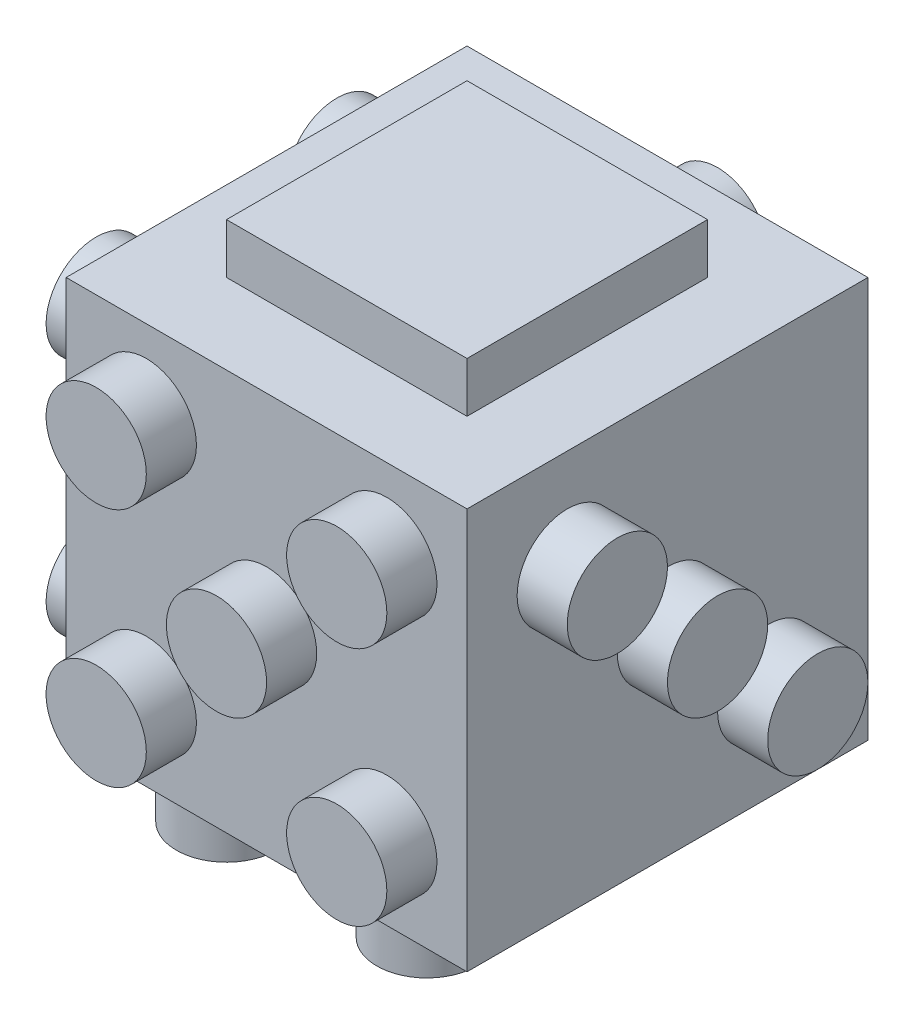
SolidWorks part; units mm, degrees
ref_plane "Front Plane" through (0, 0, 0) normal (0, 0, 1) x (1, 0, 0)
ref_plane "Top Plane" through (0, 0, 0) normal (0, 1, 0) x (1, 0, 0)
ref_plane "Right Plane" through (0, 0, 0) normal (1, 0, 0) x (0, 0, -1)
sketch "Sketch1" plane through (0, 0, 0) normal (0, 1, 0) x (1, 0, 0)
  line L1 (-12.5, 12.5) -> (12.5, 12.5)
  line L2 (-12.5, 12.5) -> (-12.5, -12.5)
  line L3 (-12.5, -12.5) -> (12.5, -12.5)
  line L4 (12.5, 12.5) -> (12.5, -12.5)
  line L5 (0, -12.5) -> (0, 12.5) construction
  line L6 (-12.5, 0) -> (12.5, 0) construction
  point P0 (0, 0)
  dimension "D1" = 25
  dimension "D2" = 25
extrude "Boss-Extrude1" add sketch "Sketch1" along normal blind 25
sketch "Sketch2" plane through (0, 25, 0) normal (0, 1, 0) x (1, 0, 0)
  line L1 (-6, 6) -> (6, 6)
  line L2 (-6, 6) -> (-6, -6)
  line L3 (-6, -6) -> (6, -6)
  line L4 (6, 6) -> (6, -6)
  line L5 (0, -6) -> (0, 6) construction
  line L6 (-6, 0) -> (6, 0) construction
  point P0 (0, 0)
  dimension "D1" = 12
  dimension "D2" = 12
sketch "Sketch3" plane through (0, 0, 0) normal (0, -1, 0) x (1, 0, 0)
  line L1 (10, 10) -> (-10, 10) construction
  line L2 (10, 10) -> (10, -10) construction
  line L3 (10, -10) -> (-10, -10) construction
  line L4 (-10, 10) -> (-10, -10) construction
  line L5 (0, -10) -> (0, 10) construction
  line L6 (10, 0) -> (-10, 0) construction
  line L7 (5, -7) -> (-5, -7) construction
  line L8 (5, -7) -> (5, 7) construction
  line L9 (5, 7) -> (-5, 7) construction
  line L10 (-5, -7) -> (-5, 7) construction
  line L11 (0, 7) -> (0, -7) construction
  line L12 (5, 0) -> (-5, 0) construction
  circle A0 centre (-5, 7) radius 2.5
  circle A1 centre (-5, 0) radius 2.5
  circle A2 centre (-5, -7) radius 2.5
  circle A3 centre (5, 7) radius 2.5
  circle A4 centre (5, 0) radius 2.5
  circle A5 centre (5, -7) radius 2.5
  point P0 (0, 0)
  point P4 (0, 0)
  dimension "D5" = 5
  dimension "D6" = 5
  dimension "D7" = 5
  dimension "D8" = 5
  dimension "D1" = 20
  dimension "D2" = 20
  dimension "D3" = 10
  dimension "D4" = 14
sketch "Sketch4" plane through (12.5, 0, 0) normal (1, 0, 0) x (0, 0, -1)
  line L4 (-12.5, 0) -> (12.5, 0)
  line L5 (12.5, 0) -> (12.5, 25)
  line L6 (12.5, 25) -> (-12.5, 25)
  line L7 (-12.5, 25) -> (-12.5, 0)
  line L8 (-12.5, 0) -> (12.5, 0)
  line L10 (12.5, 25) -> (-12.5, 25)
  line L11 (-12.5, 25) -> (-12.5, 0)
  circle A0 centre (-5, 17.5) radius 2.5
  circle A1 centre (0, 12.5) radius 2.5
  circle A2 centre (5, 7.5) radius 2.5
  dimension "D5" = 5
  dimension "D6" = 5
  dimension "D7" = 5
  dimension "D1" = 0
sketch "Sketch5" plane through (-12.5, 0, 0) normal (-1, 0, 0) x (0, 0, 1)
  line L0 (-12.5, 12.5) -> (0, 12.5) construction
  line L2 (-10, 22.5) -> (10, 22.5) construction
  line L3 (-10, 22.5) -> (-10, 2.5) construction
  line L4 (-12.5, 0) -> (12.5, 0)
  line L5 (12.5, 0) -> (12.5, 25)
  line L6 (12.5, 25) -> (-12.5, 25)
  line L7 (-12.5, 25) -> (-12.5, 0)
  line L8 (-12.5, 0) -> (12.5, 0)
  line L9 (12.5, 0) -> (12.5, 25)
  line L10 (12.5, 25) -> (-12.5, 25)
  line L11 (-12.5, 25) -> (-12.5, 0)
  line L12 (-10, 2.5) -> (10, 2.5) construction
  line L13 (10, 22.5) -> (10, 2.5) construction
  line L14 (0, 2.5) -> (0, 22.5) construction
  line L15 (-10, 12.5) -> (10, 12.5) construction
  line L16 (-6, 18.5) -> (6, 18.5) construction
  line L17 (-6, 18.5) -> (-6, 6.5) construction
  line L18 (-6, 6.5) -> (6, 6.5) construction
  line L19 (6, 18.5) -> (6, 6.5) construction
  line L20 (0, 6.5) -> (0, 18.5) construction
  line L21 (-6, 12.5) -> (6, 12.5) construction
  circle A0 centre (-6, 18.5) radius 2.5
  circle A1 centre (6, 18.5) radius 2.5
  circle A2 centre (6, 6.5) radius 2.5
  circle A3 centre (-6, 6.5) radius 2.5
  dimension "D6" = 5
  dimension "D7" = 5
  dimension "D8" = 5
  dimension "D9" = 5
  dimension "D2" = 20
  dimension "D3" = 20
  dimension "D4" = 12
  dimension "D5" = 12
  dimension "D1" = 0
sketch "Sketch7" plane through (0, 0, 12.5) normal (0, 0, 1) x (1, 0, 0)
  line L0 (0, 25) -> (0, 12.5) construction
  line L2 (-10, 22.5) -> (10, 22.5) construction
  line L3 (-10, 22.5) -> (-10, 2.5) construction
  line L4 (-12.5, 0) -> (12.5, 0)
  line L5 (12.5, 0) -> (12.5, 25)
  line L6 (12.5, 25) -> (-12.5, 25)
  line L7 (-12.5, 25) -> (-12.5, 0)
  line L8 (-12.5, 0) -> (12.5, 0)
  line L9 (12.5, 0) -> (12.5, 25)
  line L10 (12.5, 25) -> (-12.5, 25)
  line L11 (-12.5, 25) -> (-12.5, 0)
  line L12 (-10, 2.5) -> (10, 2.5) construction
  line L13 (10, 22.5) -> (10, 2.5) construction
  line L14 (0, 2.5) -> (0, 22.5) construction
  line L15 (-10, 12.5) -> (10, 12.5) construction
  line L16 (-6, 18.5) -> (6, 18.5) construction
  line L17 (-6, 18.5) -> (-6, 6.5) construction
  line L18 (-6, 6.5) -> (6, 6.5) construction
  line L19 (6, 18.5) -> (6, 6.5) construction
  line L20 (0, 6.5) -> (0, 18.5) construction
  line L21 (-6, 12.5) -> (6, 12.5) construction
  circle A0 centre (-6, 18.5) radius 2.5
  circle A1 centre (0, 12.5) radius 2.5
  circle A2 centre (6, 18.5) radius 2.5
  circle A3 centre (6, 6.5) radius 2.5
  circle A4 centre (-6, 6.5) radius 2.5
  dimension "D7" = 5
  dimension "D8" = 5
  dimension "D9" = 5
  dimension "D10" = 5
  dimension "D11" = 5
  dimension "D2" = 12.5
  dimension "D3" = 20
  dimension "D4" = 20
  dimension "D5" = 12
  dimension "D6" = 12
  dimension "D1" = 0
sketch "Sketch8" plane through (0, 0, -12.5) normal (0, 0, -1) x (-1, 0, 0)
  line L0 (0, 0) -> (0, 12.5) construction
  line L1 (10, 22.5) -> (-10, 2.5) construction
  line L2 (-10, 22.5) -> (10, 22.5) construction
  line L3 (-10, 22.5) -> (-10, 2.5) construction
  line L4 (-12.5, 0) -> (12.5, 0)
  line L5 (12.5, 0) -> (12.5, 25)
  line L6 (12.5, 25) -> (-12.5, 25)
  line L7 (-12.5, 25) -> (-12.5, 0)
  line L8 (-12.5, 0) -> (12.5, 0)
  line L9 (12.5, 0) -> (12.5, 25)
  line L10 (12.5, 25) -> (-12.5, 25)
  line L11 (-12.5, 25) -> (-12.5, 0)
  line L12 (-10, 2.5) -> (10, 2.5) construction
  line L13 (10, 22.5) -> (10, 2.5) construction
  line L14 (0, 2.5) -> (0, 22.5) construction
  line L15 (-10, 12.5) -> (10, 12.5) construction
  line L17 (-6, 18.5) -> (6, 18.5) construction
  line L18 (-6, 18.5) -> (-6, 6.5) construction
  line L19 (-6, 6.5) -> (6, 6.5) construction
  line L20 (6, 18.5) -> (6, 6.5) construction
  line L21 (0, 6.5) -> (0, 18.5) construction
  line L22 (-6, 12.5) -> (6, 12.5) construction
  circle A4 centre (0, 18.5) radius 2.5
  circle A5 centre (0, 6.5) radius 2.5
  dimension "D7" = 5
  dimension "D8" = 5
  dimension "D2" = 12.5
  dimension "D3" = 20
  dimension "D4" = 20
  dimension "D5" = 12
  dimension "D6" = 12
  dimension "D1" = 0
scale "Scale1" bodies to scale 111 scale about centroid uniform scaling yes scale factor 0.8
extrude "Boss-Extrude2" add sketch "Sketch3" against normal up to surface (2.5 mm away) separate body contours A2 | A1 | A0 | A5 | A4 | A3 up to face at (0, 2.5, 0)
extrude "Boss-Extrude3" add sketch "Sketch7" against normal up to surface (2.5 mm away) contours A0 | A2 | A1 | A4 | A3 up to face at (0, 12.5, 10)
extrude "Boss-Extrude4" add sketch "Sketch5" against normal up to surface (2.5 mm away) contours A3 | A2 | A1 | A0 up to face at (-10, 12.5, 0)
extrude "Boss-Extrude5" add sketch "Sketch4" against normal up to surface (2.5 mm away) contours A2 | A1 | A0 up to face at (10, 12.5, 0)
extrude "Boss-Extrude7" add sketch "Sketch2" against normal up to surface (2.5 mm away) contours L4 L3 L2 L1 up to face at (0, 22.5, 0)
extrude "Boss-Extrude8" add sketch "Sketch8" against normal blind 10 contours A5 | A4
